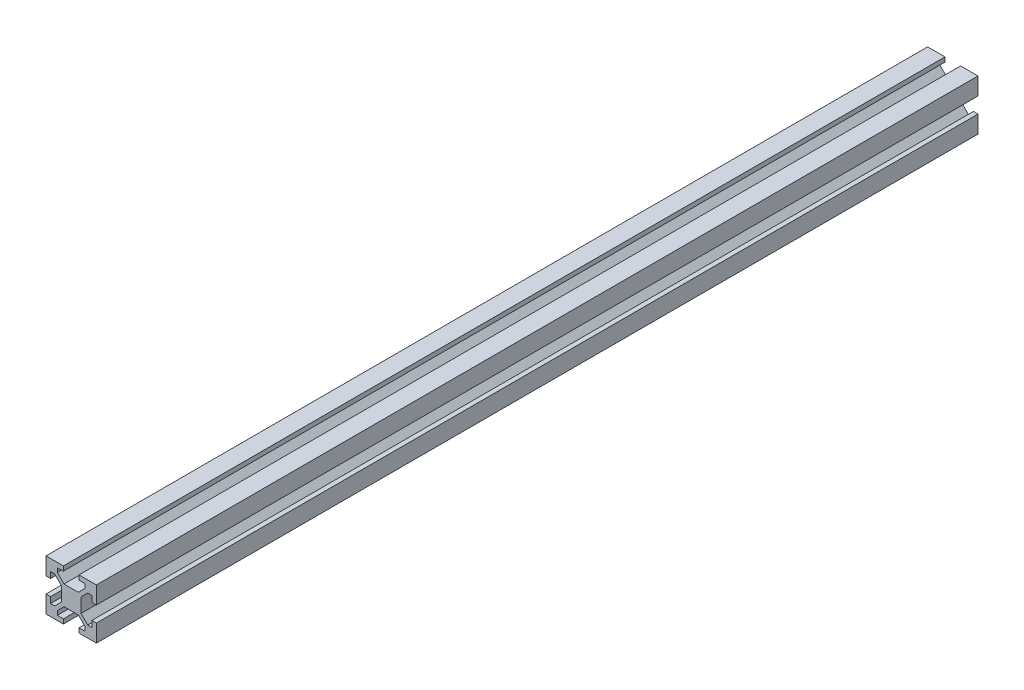
SolidWorks part; units mm, degrees
ref_plane "Front Plane" through (0, 0, 0) normal (0, 0, 1) x (1, 0, 0)
ref_plane "Top Plane" through (0, 0, 0) normal (0, 1, 0) x (1, 0, 0)
ref_plane "Right Plane" through (0, 0, 0) normal (1, 0, 0) x (0, 0, -1)
sketch "Sketch1" plane through (0, 0, 0) normal (0, 0, 1) x (1, 0, 0)
  line L0 (-3.1, 10) -> (-3.1, 8.2007)
  line L1 (-10, 10) -> (-3.1, 10)
  line L2 (-10, 10) -> (-10, 3.1)
  line L3 (-10, -10) -> (-3.1, -10)
  line L4 (10, 10) -> (10, 3.1)
  line L5 (-10, 10) -> (10, -10) construction
  line L6 (-10, -10) -> (10, 10) construction
  line L7 (-3.1, 8.2007) -> (-5.5, 8.2007)
  line L8 (-5.5, 8.2007) -> (-5.5, 6.5607)
  line L9 (-5.5, 6.5607) -> (-2.84, 3.9007)
  line L10 (-2.84, 3.9007) -> (2.84, 3.9007)
  line L11 (2.84, 3.9007) -> (5.5, 6.5607)
  line L12 (5.5, 6.5607) -> (5.5, 8.2007)
  line L13 (5.5, 8.2007) -> (3.1, 8.2007)
  line L14 (3.1, 8.2007) -> (3.1, 10)
  line L15 (-3.1, 8.2007) -> (3.1, 8.2007) construction
  line L16 (-5.5, 6.5607) -> (5.5, 6.5607) construction
  line L17 (3.1, 10) -> (10, 10)
  line L18 (8.2007, 3.1) -> (8.2007, 5.5)
  line L19 (8.2007, 5.5) -> (6.5607, 5.5)
  line L20 (6.5607, 5.5) -> (3.9007, 2.84)
  line L21 (3.9007, 2.84) -> (3.9007, -2.84)
  line L22 (3.9007, -2.84) -> (6.5607, -5.5)
  line L23 (6.5607, -5.5) -> (8.2007, -5.5)
  line L24 (8.2007, -5.5) -> (8.2007, -3.1)
  line L25 (8.2007, 3.1) -> (8.2007, -3.1) construction
  line L26 (6.5607, 5.5) -> (6.5607, -5.5) construction
  line L27 (10, 3.1) -> (8.2007, 3.1)
  line L28 (8.2007, -3.1) -> (10, -3.1)
  line L29 (3.1, -8.2007) -> (5.5, -8.2007)
  line L30 (5.5, -8.2007) -> (5.5, -6.5607)
  line L31 (5.5, -6.5607) -> (2.84, -3.9007)
  line L32 (2.84, -3.9007) -> (-2.84, -3.9007)
  line L33 (-2.84, -3.9007) -> (-5.5, -6.5607)
  line L34 (-5.5, -6.5607) -> (-5.5, -8.2007)
  line L35 (-5.5, -8.2007) -> (-3.1, -8.2007)
  line L36 (3.1, -8.2007) -> (-3.1, -8.2007) construction
  line L37 (5.5, -6.5607) -> (-5.5, -6.5607) construction
  line L38 (3.1, -10) -> (3.1, -8.2007)
  line L39 (-3.1, -8.2007) -> (-3.1, -10)
  line L40 (-8.2007, -3.1) -> (-8.2007, -5.5)
  line L41 (-8.2007, -5.5) -> (-6.5607, -5.5)
  line L42 (-6.5607, -5.5) -> (-3.9007, -2.84)
  line L43 (-3.9007, -2.84) -> (-3.9007, 2.84)
  line L44 (-3.9007, 2.84) -> (-6.5607, 5.5)
  line L45 (-6.5607, 5.5) -> (-8.2007, 5.5)
  line L46 (-8.2007, 5.5) -> (-8.2007, 3.1)
  line L47 (-8.2007, -3.1) -> (-8.2007, 3.1) construction
  line L48 (-6.5607, -5.5) -> (-6.5607, 5.5) construction
  line L49 (-10, -3.1) -> (-8.2007, -3.1)
  line L50 (-8.2007, 3.1) -> (-10, 3.1)
  line L51 (10, -3.1) -> (10, -10)
  line L52 (3.1, -10) -> (10, -10)
  line L53 (-10, -3.1) -> (-10, -10)
  point P0 (0, 0)
  point P8 (0, 8.2007)
  point P18 (0, 3.9007)
  dimension "D1" = 20
  dimension "D2" = 20
  dimension "D3" = 5.68
  dimension "D4" = 6.2
  dimension "D5" = 4.3
  dimension "D6" = 11
  dimension "D7" = 0.75
  dimension "D8" = 4
extrude "Boss-Extrude1" add sketch "Sketch1" along normal mid plane 350
